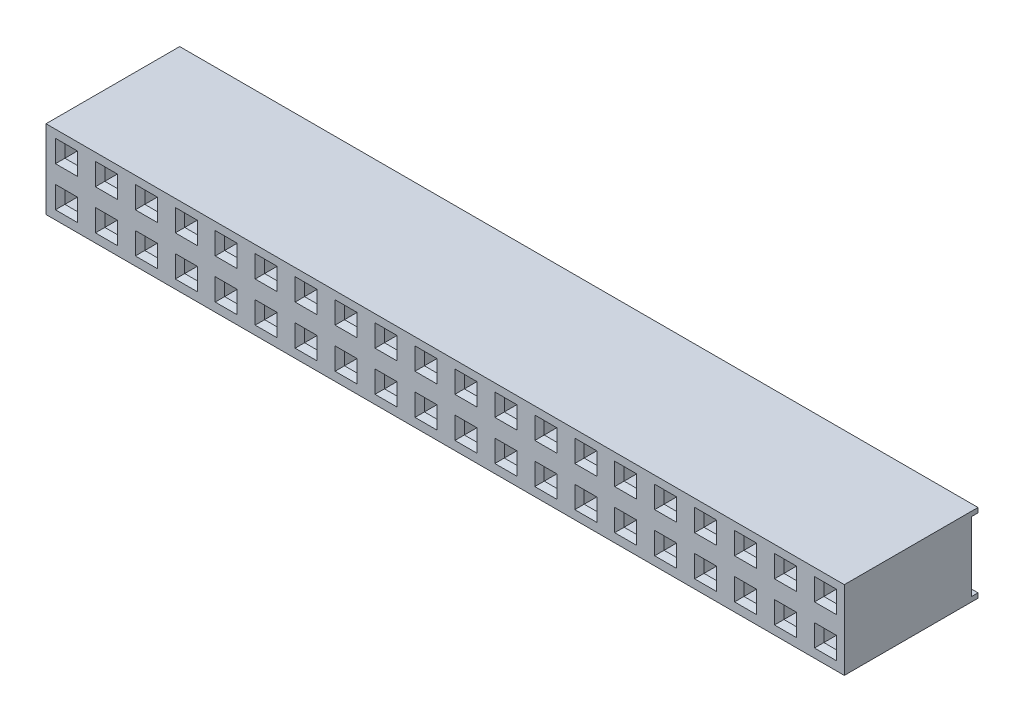
SolidWorks part; units mm, degrees
material "ABS"
ref_plane "Front Plane" through (0, 0, 0) normal (0, 0, 1) x (1, 0, 0)
ref_plane "Top Plane" through (0, 0, 0) normal (0, 1, 0) x (1, 0, 0)
ref_plane "Right Plane" through (0, 0, 0) normal (1, 0, 0) x (0, 0, -1)
sketch "Sketch1" plane through (0, 0, 0) normal (1, 0, 0) x (0, 0, -1)
  line L16 (8.5, 5) -> (0, 5)
  line L17 (0, 5) -> (0, 0)
  line L18 (0, 0) -> (8.5, 0)
  line L19 (8.5, 0) -> (8.5, 0.3)
  line L20 (8.5, 0.3) -> (8.1, 0.3)
  line L21 (8.1, 0.3) -> (8.1, 4.7)
  line L22 (8.1, 4.7) -> (8.5, 4.7)
  line L23 (8.5, 4.7) -> (8.5, 5)
  dimension "D2" = 0.3
  dimension "D3" = 0.4
  dimension "D4" = 8.5
  dimension "D5" = 5
extrude "Boss-Extrude1" add sketch "Sketch1" against normal blind 50.76 separate body
sketch "Sketch2" plane through (0, 0, -8.1) normal (0, 0, -1) x (-1, 0, 0)
  line L0 (50.76, 5) -> (0, 5) construction
  line L3 (2, 3.6) -> (2, 4.2)
  line L4 (2, 3.6) -> (0.4, 3.6)
  line L5 (0.4, 3.6) -> (0.4, 4.2)
  line L6 (2, 4.2) -> (0.4, 4.2)
  line L8 (0, 0.3) -> (0, 4.7) construction
  dimension "D1" = 0.6
  dimension "D2" = 0.4
  dimension "D3" = 1.6
  dimension "D4" = 0.8
extrude "Cut-Extrude1" cut sketch "Sketch2" against normal blind 2
sketch "Sketch3" plane through (0, 0, 0) normal (0, 0, -1) x (-1, 0, 0)
  line L1 (2, 4.2) -> (0.4, 4.2) construction
  line L4 (0.8, 4.2) -> (1.6, 4.2)
  line L5 (0.8, 3.4) -> (0.8, 4.2)
  line L6 (1.6, 3.4) -> (0.8, 3.4)
  line L7 (1.6, 4.2) -> (1.6, 3.4)
  point P4 (1.2, 4.2)
  dimension "D1" = 0.8
extrude "Cut-Extrude2" cut sketch "Sketch3" along normal blind 2.5
sketch "Sketch4" plane through (0, 0, 0) normal (0, 0, 1) x (1, 0, 0)
  line L4 (-0.5, 4.5) -> (-1.9, 4.5)
  line L5 (-0.5, 4.5) -> (-1.9, 4.5)
  line L31 (-0.5, 3.1) -> (-0.5, 4.5)
  line L32 (-1.9, 3.1) -> (-0.5, 3.1)
  line L33 (-1.9, 4.5) -> (-1.9, 3.1)
  line L35 (-0.5, 3.1) -> (-0.5, 4.5)
  line L36 (-1.9, 3.1) -> (-0.5, 3.1)
  line L37 (-1.9, 4.5) -> (-1.9, 3.1)
  dimension "D1" = 0.3
extrude "Cut-Extrude3" cut sketch "Sketch4" against normal blind 0.5 draft 45
pattern_linear "LPattern1" count 25 spacing 2.54 along (-1, 0, 0) count 3 spacing 2.54 along (0, -1, 0) of "Cut-Extrude2", "Cut-Extrude1", "Cut-Extrude3"
equation "\"Pin Number\"= 20"
equation "\"Pitch\"=2.54"
equation "\"D4@LPattern1\" = \"Pitch\""
equation "\"D3@LPattern1\" = \"Pitch\""
equation "\"D2@LPattern1\" = \"Pitch\""
equation "\"D1@LPattern1\" = \"Pin Number\" / 2"
equation "\"Pin Number\"= \"D1@Boss-Extrude1\""
